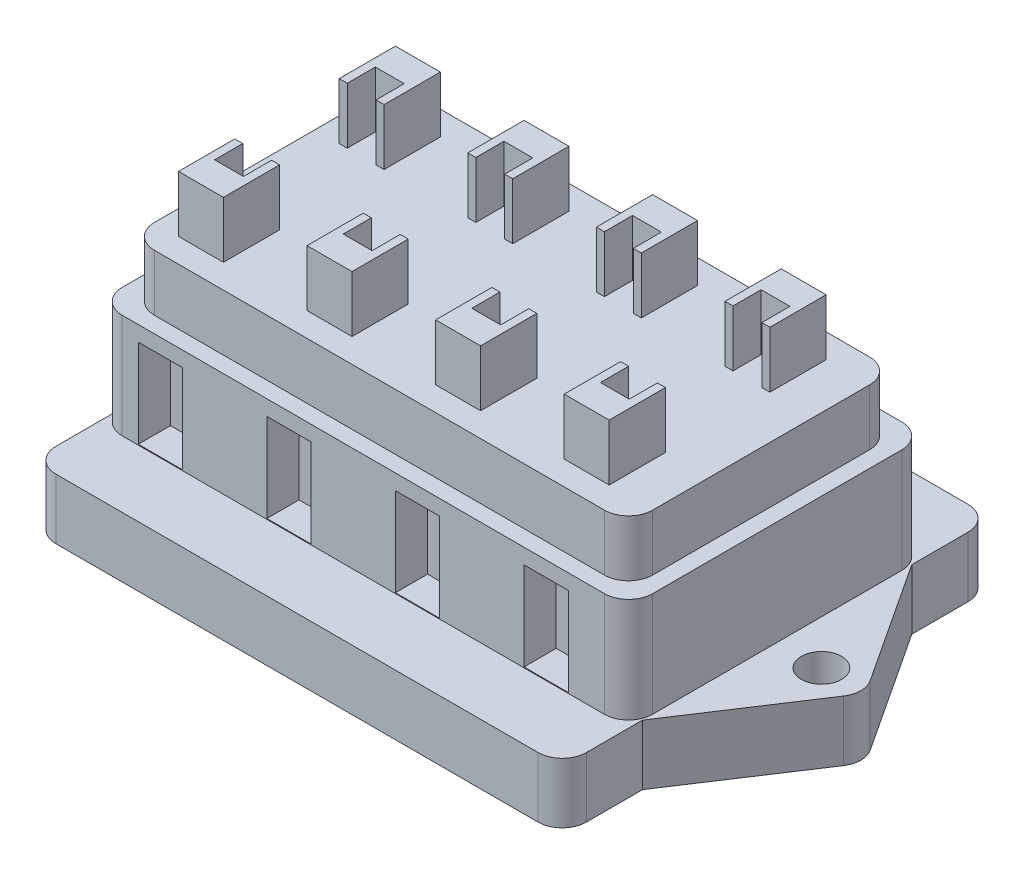
SolidWorks part; units mm, degrees
ref_plane "Front Plane" through (0, 0, 0) normal (0, 0, 1) x (1, 0, 0)
ref_plane "Top Plane" through (0, 0, 0) normal (0, 1, 0) x (1, 0, 0)
ref_plane "Right Plane" through (0, 0, 0) normal (1, 0, 0) x (0, 0, -1)
sketch "Sketch1" plane through (0, 0, 0) normal (0, 1, 0) x (1, 0, 0)
  line L0 (33, 16.75) -> (42.9185, 1.6468)
  line L1 (-30, 26.75) -> (30, 26.75)
  line L2 (-33, 23.75) -> (-33, 16.75)
  line L3 (-30, -26.75) -> (30, -26.75)
  line L4 (33, 23.75) -> (33, 16.75)
  line L5 (33, 37.1962) -> (33, -34.1675) construction
  line L6 (42.9185, -1.6468) -> (33, -16.75)
  line L7 (-33, 16.75) -> (-42.9185, 1.6468)
  line L8 (-42.9185, -1.6468) -> (-33, -16.75)
  line L9 (51.8837, 0) -> (-51.0633, 0) construction
  line L10 (33, -16.75) -> (33, -23.75)
  line L11 (-33, -16.75) -> (-33, -23.75)
  line L12 (0, 37.1962) -> (0, -34.1675) construction
  arc A0 (42.9185, -1.6468) -> (42.9185, 1.6468) centre (40.4109, 0) ccw
  arc A1 (-42.9185, -1.6468) -> (-42.9185, 1.6468) centre (-40.4109, 0) cw
  arc A2 (30, 26.75) -> (33, 23.75) centre (30, 23.75) cw
  arc A3 (30, -26.75) -> (33, -23.75) centre (30, -23.75) ccw
  arc A4 (-30, -26.75) -> (-33, -23.75) centre (-30, -23.75) cw
  arc A5 (-33, 23.75) -> (-30, 26.75) centre (-30, 23.75) cw
  circle A6 centre (38.5, 0) radius 2.5
  circle A8 centre (-38.5, 0) radius 2.5
  point P0 (0, 0)
  point P18 (33, 26.75)
  point P21 (33, -26.75)
  point P26 (-33, 26.75)
  point P35 (44, 0)
  point P38 (-44, 0)
  dimension "D2" = 11
  dimension "D3" = 53.5
  dimension "D4" = 66
  dimension "D5" = 3
  dimension "D6" = 5.5
  dimension "D7" = 5.5
  dimension "D8" = 3
  dimension "D9" = 3
  dimension "D1" = 10
extrude "Boss-Extrude1" add sketch "Sketch1" along normal blind 7.5
sketch "Sketch2" plane through (0, 7.5, 0) normal (0, 1, 0) x (1, 0, 0)
  line L0 (33, -23.75) -> (33, -16.75) construction
  line L1 (-30, 18.5) -> (30, 18.5)
  line L2 (-33, 15.5) -> (-33, -15.5)
  line L3 (-30, -18.5) -> (30, -18.5)
  line L4 (33, 15.5) -> (33, -15.5)
  line L5 (-33, 18.5) -> (33, -18.5) construction
  line L6 (-33, -18.5) -> (33, 18.5) construction
  arc A0 (33, 15.5) -> (30, 18.5) centre (30, 15.5) ccw
  arc A1 (30, -18.5) -> (33, -15.5) centre (30, -15.5) ccw
  arc A2 (-33, -15.5) -> (-30, -18.5) centre (-30, -15.5) ccw
  arc A3 (-33, 15.5) -> (-30, 18.5) centre (-30, 15.5) cw
  point P0 (0, 0)
  dimension "D2" = 3
  dimension "D1" = 37
extrude "Boss-Extrude2" add sketch "Sketch2" along normal blind 20
sketch "Sketch3" plane through (0, 27.5, 0) normal (0, 1, 0) x (1, 0, 0)
  line L0 (-33, 15.5) -> (-33, -15.5) construction
  line L1 (-28, 13.5) -> (-22.4116, 13.5)
  line L2 (-28, 13.5) -> (-28, 6.5)
  line L3 (-28, 6.5) -> (-27, 6.5)
  line L4 (-22.4116, 13.5) -> (-22.4116, 6.5)
  line L5 (-28, 13.5) -> (-22.4116, 6.5) construction
  line L6 (-28, 6.5) -> (-22.4116, 13.5) construction
  line L7 (30, 18.5) -> (-30, 18.5) construction
  line L8 (-12, 13.5) -> (-6.4116, 13.5)
  line L9 (-6.4116, 13.5) -> (-6.4116, 6.5)
  line L10 (-12, 6.5) -> (-11, 6.5)
  line L11 (-12, 13.5) -> (-12, 6.5)
  line L12 (-12, 6.5) -> (-6.4116, 13.5) construction
  line L13 (-12, 13.5) -> (-6.4116, 6.5) construction
  line L14 (4, 13.5) -> (9.5884, 13.5)
  line L15 (9.5884, 13.5) -> (9.5884, 6.5)
  line L16 (4, 6.5) -> (5, 6.5)
  line L17 (4, 13.5) -> (4, 6.5)
  line L18 (4, 6.5) -> (9.5884, 13.5) construction
  line L19 (4, 13.5) -> (9.5884, 6.5) construction
  line L20 (20, 13.5) -> (25.5884, 13.5)
  line L21 (25.5884, 13.5) -> (25.5884, 6.5)
  line L22 (20, 6.5) -> (21, 6.5)
  line L23 (20, 13.5) -> (20, 6.5)
  line L24 (20, 6.5) -> (25.5884, 13.5) construction
  line L25 (20, 13.5) -> (25.5884, 6.5) construction
  line L26 (-12, -6.5) -> (-11, -6.5)
  line L27 (-6.4116, -6.5) -> (-6.4116, -13.5)
  line L28 (-12, -13.5) -> (-6.4116, -13.5)
  line L29 (-12, -6.5) -> (-12, -13.5)
  line L30 (-12, -13.5) -> (-6.4116, -6.5) construction
  line L31 (-12, -6.5) -> (-6.4116, -13.5) construction
  line L32 (4, -6.5) -> (5, -6.5)
  line L33 (9.5884, -6.5) -> (9.5884, -13.5)
  line L34 (4, -13.5) -> (9.5884, -13.5)
  line L35 (4, -6.5) -> (4, -13.5)
  line L36 (4, -13.5) -> (9.5884, -6.5) construction
  line L37 (4, -6.5) -> (9.5884, -13.5) construction
  line L38 (20, -6.5) -> (21, -6.5)
  line L39 (25.5884, -6.5) -> (25.5884, -13.5)
  line L40 (20, -13.5) -> (25.5884, -13.5)
  line L41 (20, -6.5) -> (20, -13.5)
  line L42 (20, -13.5) -> (25.5884, -6.5) construction
  line L43 (20, -6.5) -> (25.5884, -13.5) construction
  line L44 (-28, -6.5) -> (-27, -6.5)
  line L45 (-22.4116, -6.5) -> (-22.4116, -13.5)
  line L46 (-28, -13.5) -> (-22.4116, -13.5)
  line L47 (-28, -6.5) -> (-28, -13.5)
  line L48 (-28, -13.5) -> (-22.4116, -6.5) construction
  line L49 (-28, -6.5) -> (-22.4116, -13.5) construction
  line L50 (-7.4116, 10) -> (-7.4116, 6.5)
  line L51 (-11, 10) -> (-11, 6.5)
  line L52 (-23.4116, 10) -> (-27, 10)
  line L53 (-23.4116, 10) -> (-23.4116, 6.5)
  line L54 (-7.4116, 6.5) -> (-6.4116, 6.5)
  line L55 (-27, 10) -> (-27, 6.5)
  line L56 (-7.4116, 10) -> (-11, 10)
  line L57 (8.5884, 10) -> (8.5884, 6.5)
  line L58 (5, 10) -> (5, 6.5)
  line L59 (8.5884, 10) -> (5, 10)
  line L60 (24.5884, 10) -> (24.5884, 6.5)
  line L61 (21, 10) -> (21, 6.5)
  line L62 (24.5884, 10) -> (21, 10)
  line L63 (-7.4116, -6.5) -> (-7.4116, -10)
  line L64 (-11, -6.5) -> (-11, -10)
  line L65 (-23.4116, -6.5) -> (-22.4116, -6.5)
  line L66 (8.5884, -6.5) -> (8.5884, -10)
  line L67 (5, -6.5) -> (5, -10)
  line L68 (-7.4116, -6.5) -> (-6.4116, -6.5)
  line L69 (24.5884, -6.5) -> (24.5884, -10)
  line L70 (21, -6.5) -> (21, -10)
  line L71 (8.5884, -6.5) -> (9.5884, -6.5)
  line L72 (-23.4116, -6.5) -> (-23.4116, -10)
  line L73 (-27, -6.5) -> (-27, -10)
  line L75 (-23.4116, -10) -> (-27, -10)
  line L76 (-27, -10) -> (-26.937, -10.0224)
  line L77 (-11, -10) -> (-7.4116, -10)
  line L78 (5, -10) -> (8.5884, -10)
  line L79 (21, -10) -> (24.5884, -10)
  line L80 (-23.4116, 6.5) -> (-22.4116, 6.5)
  line L81 (8.5884, 6.5) -> (9.5884, 6.5)
  line L82 (24.5884, 6.5) -> (25.5884, 6.5)
  line L83 (24.5884, -6.5) -> (25.5884, -6.5)
  line L84 (24.5884, -6.5) -> (21, -6.5) [skipped]
  line L85 (8.5884, -6.5) -> (5, -6.5) [skipped]
  line L86 (-7.4116, -6.5) -> (-11, -6.5) [skipped]
  line L87 (-23.4116, -6.5) -> (-27, -6.5) [skipped]
  point P0 (-25.2058, 10)
  dimension "D1" = 5
  dimension "D2" = 5
  dimension "D3" = 7
  dimension "D6" = 1
  dimension "D7" = 1
  dimension "D8" = 3.5884
  dimension "D4" = 4
  dimension "D5" = 2
  dimension "D9" = 4
  dimension "D10" = 2
extrude "Boss-Extrude3" add sketch "Sketch3" along normal blind 7 contours L73 L44 L47 L46 L45 L65 L72 L75 | L29 L28 L27 L68 L63 L77 L64 L26 | L35 L34 L33 L71 L66 L78 L67 L32 | L41 L40 L39 L83 L69 L79 L70 L38 | L21 L82 L60 L62 L61 L22 L23 L20 | L17 L16 L58 L59 L57 L81 L15 L14 | L9 L54 L50 L56 L51 L10 L11 L8 | L2 L3 L55 L52 L53 L80 L4 L1
sketch "Sketch4" plane through (0, 27.5, 0) normal (0, 1, 0) x (1, 0, 0)
  line L0 (30, 18.5) -> (-30, 18.5) construction
  line L1 (-28, 16.5) -> (28, 16.5)
  line L2 (-31, 13.5) -> (-31, -13.5)
  line L3 (-28, -16.5) -> (28, -16.5)
  line L4 (31, 13.5) -> (31, -13.5)
  line L5 (-30, -18.5) -> (30, -18.5) construction
  line L7 (33, -15.5) -> (33, 15.5) construction
  arc A0 (31, 13.5) -> (28, 16.5) centre (28, 13.5) ccw
  arc A1 (28, -16.5) -> (31, -13.5) centre (28, -13.5) ccw
  arc A2 (-28, -16.5) -> (-31, -13.5) centre (-28, -13.5) cw
  arc A3 (-31, 13.5) -> (-28, 16.5) centre (-28, 13.5) cw
  point P0 (0, 0)
  dimension "D3" = 3
  dimension "D1" = 2
  dimension "D2" = 2
  dimension "D4" = 2
extrude "Cut-Extrude-Thin1" cut sketch "Sketch4" against normal blind 7 from offset 0 thin thin type one direction wall 3
sketch "Sketch5" plane through (0, 0, 18.5) normal (0, 0, 1) x (1, 0, 0)
  line L1 (-28, 18.6) -> (-22.5, 18.6)
  line L2 (-28, 18.6) -> (-28, 7.6)
  line L3 (-28, 7.6) -> (-22.5, 7.6)
  line L4 (-22.5, 18.6) -> (-22.5, 7.6)
  line L6 (-33, 20.5) -> (-33, 7.5) construction
  line L9 (-12, 18.6) -> (-6.5, 18.6)
  line L10 (-6.5, 18.6) -> (-6.5, 7.6)
  line L11 (-12, 7.6) -> (-6.5, 7.6)
  line L12 (-12, 18.6) -> (-12, 7.6)
  line L13 (4, 18.6) -> (9.5, 18.6)
  line L14 (9.5, 18.6) -> (9.5, 7.6)
  line L15 (4, 7.6) -> (9.5, 7.6)
  line L16 (4, 18.6) -> (4, 7.6)
  line L17 (20, 18.6) -> (25.5, 18.6)
  line L18 (25.5, 18.6) -> (25.5, 7.6)
  line L19 (20, 7.6) -> (25.5, 7.6)
  line L20 (20, 18.6) -> (20, 7.6)
  dimension "D1" = 11
  dimension "D2" = 5
  dimension "D3" = 5.5
  dimension "D4" = 4
extrude "Cut-Extrude2" cut sketch "Sketch5" against normal blind 4
sketch "Sketch6" plane through (0, 0, -18.5) normal (0, 0, -1) x (-1, 0, 0)
  line L0 (-30, 7.5) -> (30, 7.5) construction
  line L1 (-26, 18.5) -> (-20.5, 18.5)
  line L2 (-26, 18.5) -> (-26, 7.5)
  line L3 (-26, 7.5) -> (-20.5, 7.5)
  line L4 (-20.5, 18.5) -> (-20.5, 7.5)
  line L5 (-33, 20.5) -> (-33, 7.5) construction
  line L6 (-10, 7.5) -> (-4.5, 7.5)
  line L7 (-10, 18.5) -> (-10, 7.5)
  line L8 (-10, 18.5) -> (-4.5, 18.5)
  line L9 (-4.5, 18.5) -> (-4.5, 7.5)
  line L10 (6, 7.5) -> (11.5, 7.5)
  line L11 (6, 18.5) -> (6, 7.5)
  line L12 (6, 18.5) -> (11.5, 18.5)
  line L13 (11.5, 18.5) -> (11.5, 7.5)
  line L14 (22, 7.5) -> (27.5, 7.5)
  line L15 (22, 18.5) -> (22, 7.5)
  line L16 (22, 18.5) -> (27.5, 18.5)
  line L17 (27.5, 18.5) -> (27.5, 7.5)
  dimension "D1" = 11
  dimension "D2" = 7
  dimension "D3" = 5.5
  dimension "D4" = 4
extrude "Cut-Extrude3" cut sketch "Sketch6" against normal blind 4
